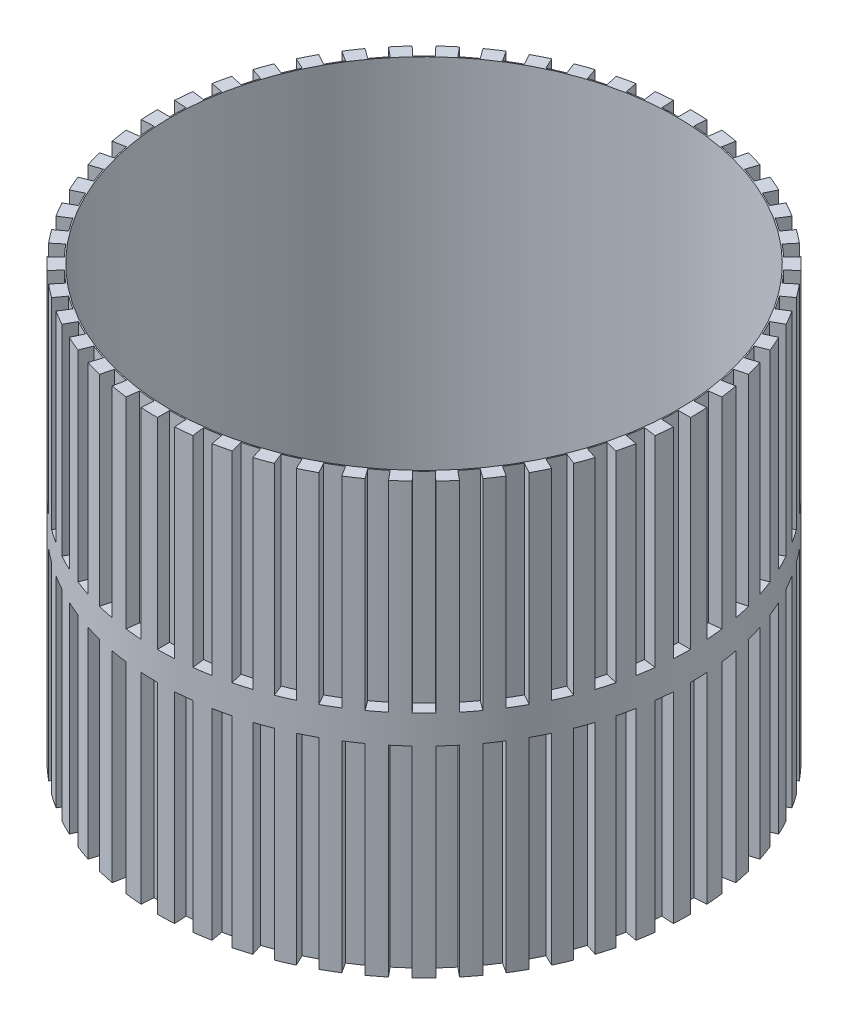
SolidWorks part; units mm, degrees
material "Полиамид ПА-6Б ТУ 6-05-988-93"
ref_plane "Спереди" through (0, 0, 0) normal (0, 0, 1) x (1, 0, 0)
ref_plane "Сверху" through (0, 0, 0) normal (0, 1, 0) x (1, 0, 0)
ref_plane "Справа" through (0, 0, 0) normal (1, 0, 0) x (0, 0, -1)
sketch "Эскиз1" plane through (0, 0, 0) normal (0, 1, 0) x (1, 0, 0)
  circle A0 centre (0, 0) radius 12.89
  dimension "D1" = 25.78
extrude "Бобышка-Вытянуть1" add sketch "Эскиз1" along normal mid plane 20.8
sketch "Эскиз4" plane through (0, 10.4, 0) normal (0, 1, 0) x (1, 0, 0)
  line L0 (0, 0) -> (0, 12.89) construction
  line L1 (0, 0) -> (0.7723, 12.2757) construction
  line L2 (0, 0) -> (1.5416, 12.203) construction
  line L3 (0.7723, 12.2757) -> (0.8094, 12.8646)
  line L4 (1.5416, 12.203) -> (1.6155, 12.7884)
  circle A0 centre (0, 0) radius 12.89 construction
  arc A1 (1.6155, 12.7884) -> (0.8094, 12.8646) centre (0, 0) ccw
  arc A2 (0.7723, 12.2757) -> (1.5416, 12.203) centre (0, 0) cw
  dimension "D3" = 12.3
  dimension "D1" = 3.6
  dimension "D2" = 3.6
sketch "Эскиз6" plane through (0, -10.4, 0) normal (0, -1, 0) x (1, 0, 0)
  line L0 (0, 0) -> (0, -12.3) construction
  line L1 (0, 0) -> (0.7723, -12.2757) construction
  line L2 (0, -12.3) -> (0, -12.89)
  line L3 (0.7723, -12.2757) -> (0.8094, -12.8646)
  arc A0 (0, -12.3) -> (0.7723, -12.2757) centre (0, 0) ccw
  circle A1 centre (0, 0) radius 12.89 construction
  arc A2 (0, -12.89) -> (0.8094, -12.8646) centre (0, 0) ccw
  dimension "D2" = 12.3
  dimension "D1" = 3.6
extrude "Вырез-Вытянуть3" cut sketch "Эскиз4" against normal blind 9.71
extrude "Вырез-Вытянуть4" cut sketch "Эскиз6" against normal blind 9.71
pattern_circular "Круговой массив4" count 50 over 360 about axis through (0, 0, 0) along (0, 1, 0) of "Вырез-Вытянуть3", "Вырез-Вытянуть4"
sketch "Эскиз8" plane through (0, 10.4, 0) normal (0, 1, 0) x (1, 0, 0)
  circle A0 centre (0, 0) radius 12.25
  dimension "D1" = 24.5
extrude "Вырез-Вытянуть5" cut sketch "Эскиз8" against normal up to surface (20.8 mm away) up to face at (0, -10.4, 0)
